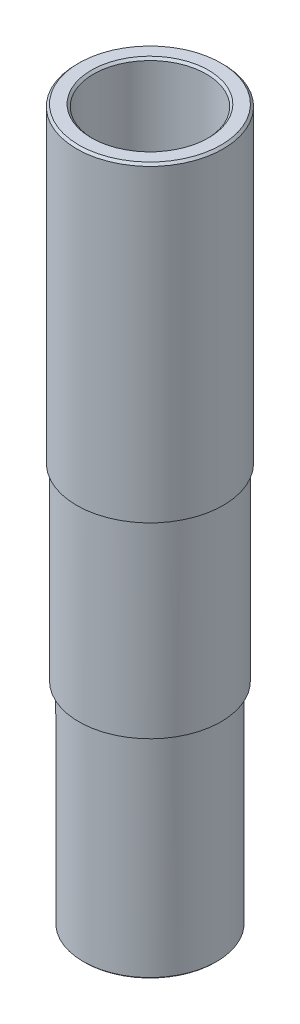
SolidWorks part; units mm, degrees
ref_plane "Front Plane" through (0, 0, 0) normal (0, 0, 1) x (1, 0, 0)
ref_plane "Top Plane" through (0, 0, 0) normal (0, 1, 0) x (1, 0, 0)
ref_plane "Right Plane" through (0, 0, 0) normal (1, 0, 0) x (0, 0, -1)
sketch "Sketch1" plane through (0, 0, 0) normal (0, 1, 0) x (1, 0, 0)
  circle A0 centre (0, 0) radius 16
  circle A1 centre (0, 0) radius 12.7
  dimension "D1" = 32
  dimension "D2" = 25.4
extrude "Boss-Extrude1" add sketch "Sketch1" along normal blind 160
sketch "Sketch2" plane through (0, 160, 0) normal (0, 1, 0) x (1, 0, 0)
  circle A0 centre (0, 0) radius 16.5
  circle A1 centre (0, 0) radius 12.7
  point P0 (-22.6025, 19.1429)
  dimension "D1" = 33
chamfer "Chamfer2" distance 0.3 angle 45 2 edges at (0, 0, 12.7) (0, 160, 12.7)
sketch "Sketch3" plane through (0, 0, 0) normal (0, -1, 0) x (1, 0, 0)
  circle A0 centre (0, 0) radius 15
  circle A1 centre (0, 0) radius 17.5
  dimension "D1" = 30
extrude "Cut-Extrude2" cut sketch "Sketch3" against normal blind 47.56
chamfer "Chamfer3" distance 0.3 angle 45 1 edges at (0, 0, -15)
extrude "Boss-Extrude3" add sketch "Sketch2" against normal blind 70
chamfer "Chamfer4" distance 0.5 angle 45 2 edges at (0, 160, 16.5) (0, 160, 12.7)
